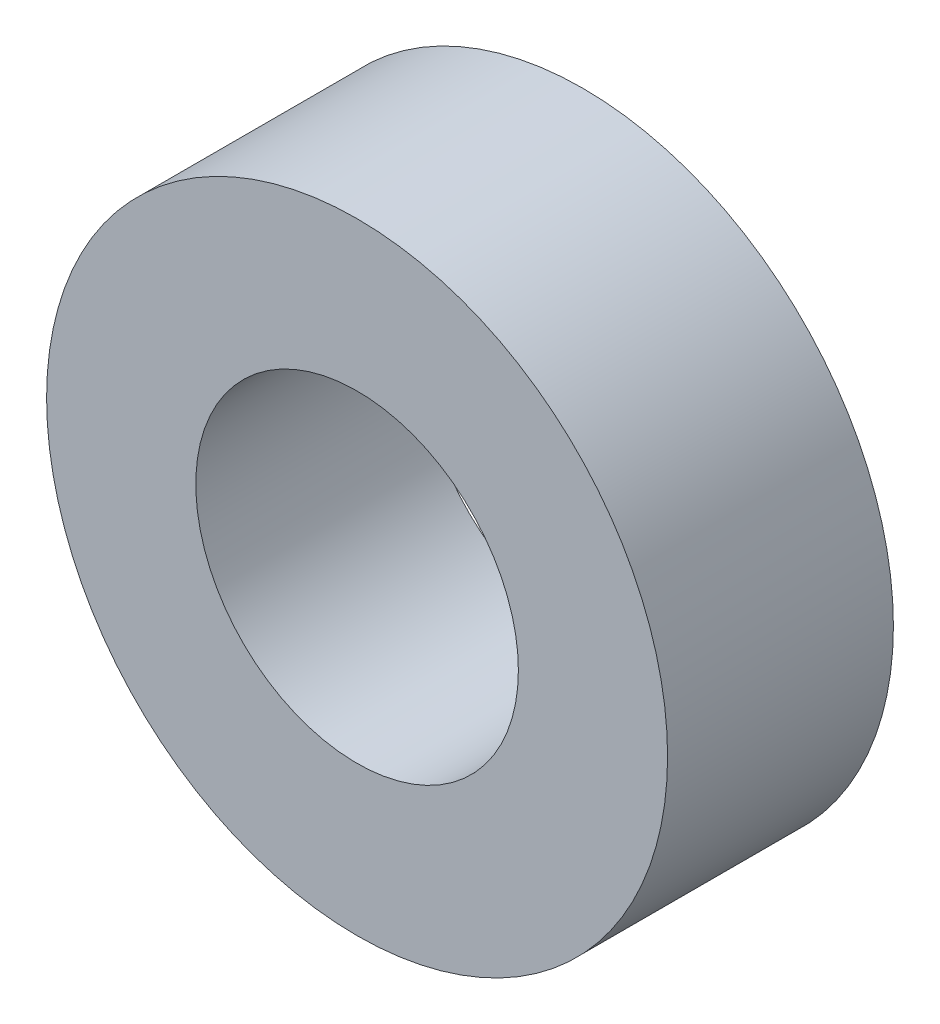
SolidWorks part; units mm, degrees
ref_plane "前基準面" through (0, 0, 0) normal (0, 0, 1) x (1, 0, 0)
ref_plane "上基準面" through (0, 0, 0) normal (0, 1, 0) x (1, 0, 0)
ref_plane "右基準面" through (0, 0, 0) normal (1, 0, 0) x (0, 0, -1)
sketch "草圖1" plane through (0, 0, 0) normal (0, 0, 1) x (1, 0, 0)
  circle A0 centre (0, 0) radius 3.85
  circle A1 centre (0, 0) radius 2
  dimension "D1" = 7.7
  dimension "D2" = 4
extrude "填料-伸長1" add sketch "草圖1" along normal blind 2.8
